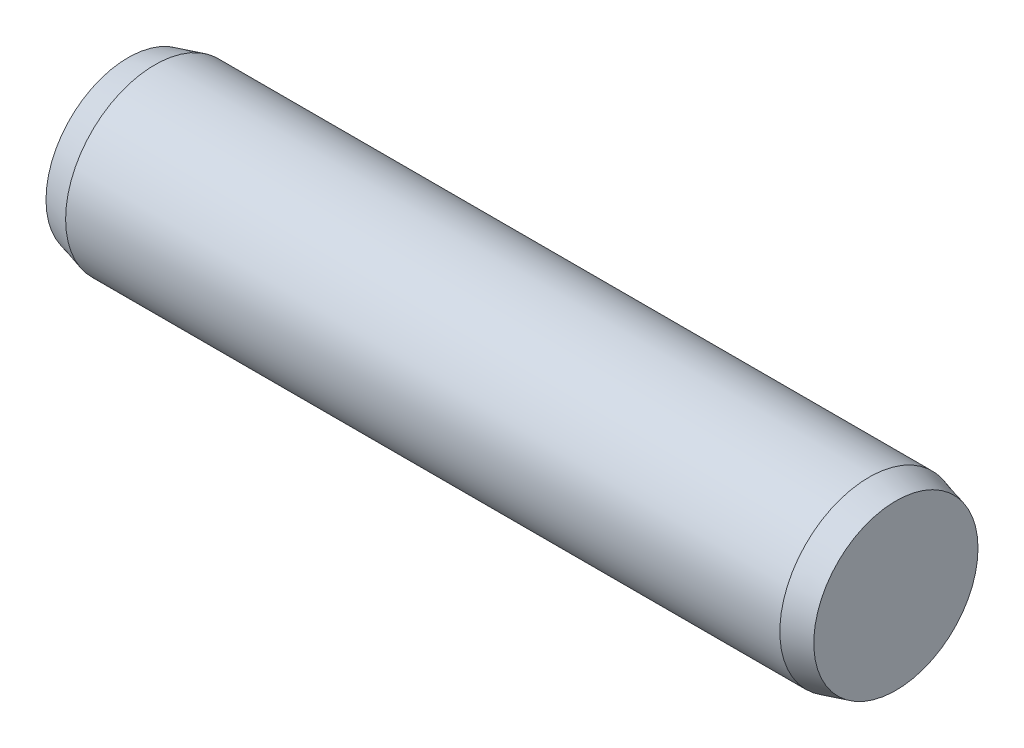
SolidWorks part; units mm, degrees
ref_plane "Front Plane" through (0, 0, 0) normal (0, 0, 1) x (1, 0, 0)
ref_plane "Top Plane" through (0, 0, 0) normal (0, 1, 0) x (1, 0, 0)
ref_plane "Right Plane" through (0, 0, 0) normal (1, 0, 0) x (0, 0, -1)
sketch "Sketch1" plane through (0, 0, 0) normal (0, 0, 1) x (1, 0, 0)
  line L0 (-8, 0) -> (8, 0) construction
  line L1 (8, 2) -> (8, -2) construction
  line L2 (-8, 2) -> (-8, -2) construction
  line L3 (8.6, 2) -> (8.6, -2) construction
  line L4 (-8.6, 2) -> (-8.6, -2) construction
  line L5 (-8, 0) -> (-8.6, 0) construction
  line L6 (8, 0) -> (8.6, 0) construction
  dimension "D1" = 0.6
  dimension "Dia" = 4
  dimension "Length" = 16
  dimension "C" = 0.6
sketch "Sketch2" plane through (0, 0, 0) normal (1, 0, 0) x (0, 0, -1)
  circle A0 centre (0, 0) radius 2
extrude "Extrude1" add sketch "Sketch2" against normal up to vertex (8 mm away) and the other way up to vertex (8 mm away) up to point (-8, 2, 0) other way up to point (8, 2, 0)
sketch "Sketch3" plane through (8, 0, 0) normal (1, 0, 0) x (0, 0, -1)
  circle A1 centre (0, 0) radius 2
  circle A2 centre (0, 0) radius 2
  dimension "D1" = 0
extrude "Extrude2" add sketch "Sketch3" along normal up to vertex (0.6 mm away) draft 15 up to point (8.6, 0, 0)
sketch "Sketch4" plane through (-8, 0, 0) normal (-1, 0, 0) x (0, 0, 1)
  circle A1 centre (0, 0) radius 2
  circle A2 centre (0, 0) radius 2
  dimension "D1" = 0
extrude "Extrude3" add sketch "Sketch4" along normal up to vertex (0.6 mm away) draft 15 up to point (-8.6, 0, 0)
equation "\"D1@Sketch1\" = \"C@Sketch1\""
